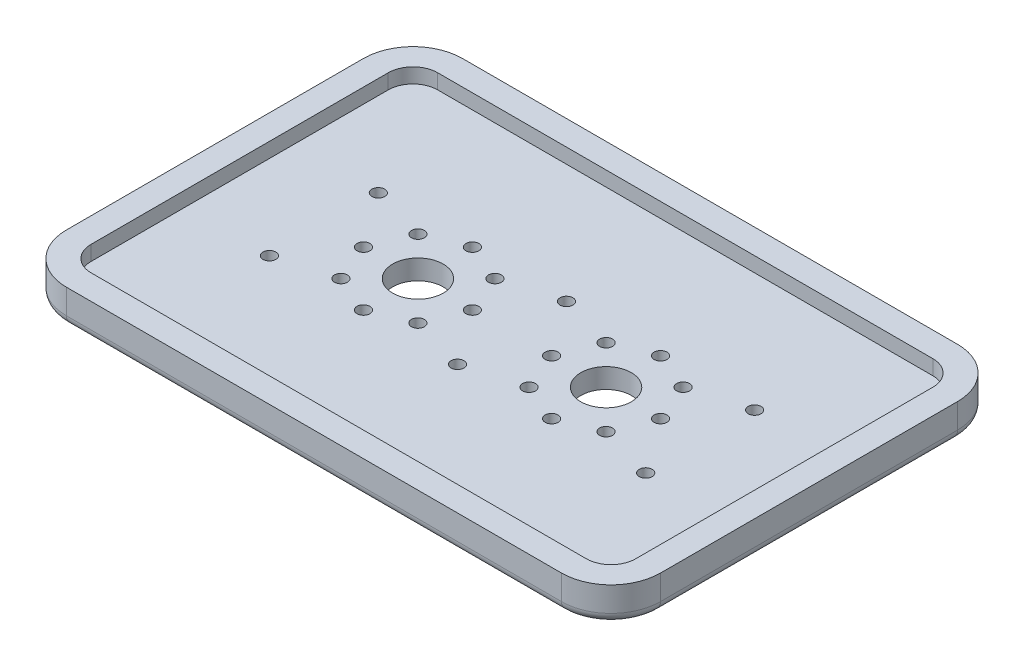
SolidWorks part; units mm, degrees
material "CA"
ref_plane "Front Plane" through (0, 0, 0) normal (0, 0, 1) x (1, 0, 0)
ref_plane "Top Plane" through (0, 0, 0) normal (0, 1, 0) x (1, 0, 0)
ref_plane "Right Plane" through (0, 0, 0) normal (1, 0, 0) x (0, 0, -1)
ref_plane "Plane1" through (0, 7, 0) normal (0, 1, 0) x (1, 0, 0)
sketch "Sketch1" plane through (0, 7, 0) normal (0, 1, 0) x (1, 0, 0)
  line L0 (-60, -40) -> (60, -40)
  line L1 (60, -40) -> (60, 40)
  line L2 (60, 40) -> (-60, 40)
  line L3 (-60, 40) -> (-60, -40)
extrude "Boss-Extrude1" add sketch "Sketch1" against normal blind 7
sketch "Sketch2" plane through (0, 7, 0) normal (0, 1, 0) x (-1, 0, 0)
  line L0 (55, 35) -> (-55, 35)
  line L1 (-55, 35) -> (-55, -35)
  line L2 (-55, -35) -> (55, -35)
  line L3 (55, -35) -> (55, 35)
extrude "Cut-Extrude1" cut sketch "Sketch2" against normal blind 3
hole_wizard "Ø2.6 (2.6) Diameter Hole1" positions "Sketch4" profile "Sketch3" hole size "Ø2.6" standard "ANSI Metric"
sketch "Sketch4" plane through (0, 4, 0) normal (0, 1, 0) x (1, 0, 0)
  point P0 (-38, -11)
  point P1 (0, 11)
  point P2 (-11.2218, -7.7782)
  point P3 (-19, -11)
  point P4 (-26.7782, -7.7782)
  point P5 (-26.7782, 7.7782)
  point P6 (-19, 11)
  point P7 (-11.2218, 7.7782)
  point P8 (11.2218, 7.7782)
  point P9 (19, 11)
  point P10 (26.7782, 7.7782)
  point P11 (30, 0)
  point P12 (26.7782, -7.7782)
  point P13 (19, -11)
  point P14 (11.2218, -7.7782)
  point P15 (-8, 0)
sketch "Sketch3" plane through (-38, 4, 11) normal (1, 0, 0) x (0, 0, 1)
  line L0 (0, 0) -> (0, 4)
  line L1 (0, 4) -> (1.3, 4)
  line L2 (1.3, 4) -> (1.3, 0)
  line L5 (1.3, 0) -> (0, 0)
  line L11 (0, -6.35) -> (0, 107.95) construction
  dimension "Thru Hole Dia." = 2.6
  dimension "Thru Hole Depth" = 4
hole_wizard "Ø10.2 (10.2) Diameter Hole1" positions "Sketch6" profile "Sketch5" hole size "Ø10.2" standard "ANSI Metric"
sketch "Sketch6" plane through (0, 4, 0) normal (0, 1, 0) x (1, 0, 0)
  point P0 (19, 0)
  point P1 (-19, 0)
sketch "Sketch5" plane through (19, 4, 0) normal (1, 0, 0) x (0, 0, 1)
  line L0 (0, 0) -> (0, 4)
  line L1 (0, 4) -> (5.1, 4)
  line L2 (5.1, 4) -> (5.1, 0)
  line L5 (5.1, 0) -> (0, 0)
  line L11 (0, -6.35) -> (0, 107.95) construction
  dimension "Thru Hole Dia." = 10.2
  dimension "Thru Hole Depth" = 4
hole_wizard "CBORE for M2 Hex Head Machine Screw1" positions "Sketch8" profile "Sketch7" counterbore size "M2" standard "ANSI Metric"
sketch "Sketch8" plane through (0, 0, 0) normal (0, -1, 0) x (-1, 0, 0)
  point P0 (-8, 0)
  point P1 (30, 0)
  point P2 (38, 11)
  point P3 (-38, 11)
  point P4 (0, -11)
  point P5 (-38, -11)
sketch "Sketch7" plane through (8, 0, 0) normal (1, 0, 0) x (0, 0, -1)
  line L0 (0, 0) -> (0, 7)
  line L1 (0, 7) -> (1.3, 7)
  line L3 (1.3, 7) -> (1.3, 1.5)
  line L4 (1.3, 1.5) -> (2.5, 1.5)
  line L5 (2.5, 1.5) -> (2.5, 0)
  line L7 (2.5, 0) -> (0, 0)
  line L11 (0, -6.35) -> (0, 107.95) construction
  dimension "Thru Hole Dia." = 2.6
  dimension "Thru Hole Depth" = 7
  dimension "C'Bore Dia." = 5
  dimension "C'Bore Depth" = 1.5
fillet "Fillet1" radius 10 4 edges at (-60, 3.5, 40) (-60, 3.5, -40) (60, 3.5, -40) (60, 3.5, 40)
fillet "Fillet2" radius 2 8 edges at (-60, 0, 0) (-57.0711, 0, -37.0711) (-57.0711, 0, 37.0711) (0, 0, -40) (0, 0, 40) (57.0711, 0, -37.0711) (57.0711, 0, 37.0711) (60, 0, 0)
fillet "Fillet3" radius 5 4 edges at (-55, 5.5, -35) (55, 5.5, -35) (55, 5.5, 35) (-55, 5.5, 35)
